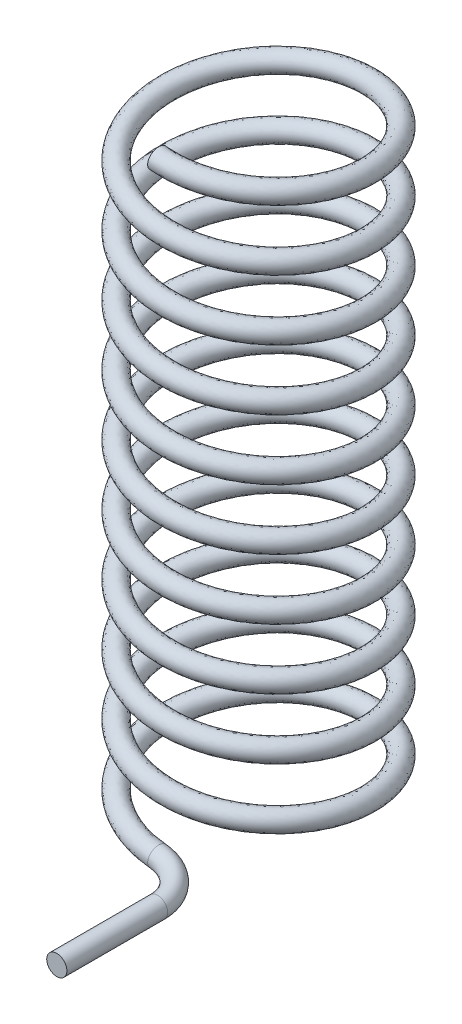
SolidWorks part; units mm, degrees
ref_plane "Ebene vorne" through (0, 0, 0) normal (0, 0, 1) x (1, 0, 0)
ref_plane "Ebene oben" through (0, 0, 0) normal (0, 1, 0) x (1, 0, 0)
ref_plane "Ebene rechts" through (0, 0, 0) normal (1, 0, 0) x (0, 0, -1)
sketch "Skizze2" plane through (0, 0, 0) normal (0, 1, 0) x (1, 0, 0)
  circle A0 centre (0, 0) radius 5
  dimension "D1" = 10
curve "Spirale/Helix1" pitch 3 height 30 turns 10
sketch3d "3D-Skizze1"
  line L1 (1.9909, -0.1901, 7) -> (1.9909, -0.1901, 12)
  arc A0 (0, 0, 5) -> (1.9909, -0.1901, 7) centre (0, 0, 7) ccw
  spline S0 degree 3 poles (-1863.284, 24.4247, -713.0203) (93.82, -4.129, -108.9377) (15.6967, -1.8024, 16.5579) (-3.6271, 0.375, 3.6276) (-4.7398, 0.5625, 1.9632) (-5.1301, 0.75, 0) (-4.7397, 0.9375, -1.9632) (-3.6276, 1.125, -3.6276) (-1.9632, 1.3125, -4.7397) (0, 1.5, -5.1302) (1.9632, 1.6875, -4.7397) (3.6276, 1.875, -3.6276) (4.7397, 2.0625, -1.9632) (5.1302, 2.25, 0) (4.7397, 2.4375, 1.9632) (3.6276, 2.625, 3.6276) (1.9632, 2.8125, 4.7397) (0, 3, 5.1302) (-1.9632, 3.1875, 4.7397) (-3.6276, 3.375, 3.6276) (-4.7397, 3.5625, 1.9632) (-5.1302, 3.75, 0) (-4.7397, 3.9375, -1.9632) (-3.6276, 4.125, -3.6276) (-1.9632, 4.3125, -4.7397) (0, 4.5, -5.1302) (1.9632, 4.6875, -4.7397) (3.6276, 4.875, -3.6276) (4.7397, 5.0625, -1.9632) (5.1302, 5.25, 0) (4.7397, 5.4375, 1.9632) (3.6276, 5.625, 3.6276) (1.9632, 5.8125, 4.7397) (0, 6, 5.1302) (-1.9632, 6.1875, 4.7397) (-3.6276, 6.375, 3.6276) (-4.7397, 6.5625, 1.9632) (-5.1302, 6.75, 0) (-4.7397, 6.9375, -1.9632) (-3.6276, 7.125, -3.6276) (-1.9632, 7.3125, -4.7397) (0, 7.5, -5.1302) (1.9632, 7.6875, -4.7397) (3.6276, 7.875, -3.6276) (4.7397, 8.0625, -1.9632) (5.1302, 8.25, 0) (4.7397, 8.4375, 1.9632) (3.6276, 8.625, 3.6276) (1.9632, 8.8125, 4.7397) (0, 9, 5.1302) (-1.9632, 9.1875, 4.7397) (-3.6276, 9.375, 3.6276) (-4.7397, 9.5625, 1.9632) (-5.1302, 9.75, 0) (-4.7397, 9.9375, -1.9632) (-3.6276, 10.125, -3.6276) (-1.9632, 10.3125, -4.7397) (0, 10.5, -5.1302) (1.9632, 10.6875, -4.7397) (3.6276, 10.875, -3.6276) (4.7397, 11.0625, -1.9632) (5.1302, 11.25, 0) (4.7397, 11.4375, 1.9632) (3.6276, 11.625, 3.6276) (1.9632, 11.8125, 4.7397) (0, 12, 5.1302) (-1.9632, 12.1875, 4.7397) (-3.6276, 12.375, 3.6276) (-4.7397, 12.5625, 1.9632) (-5.1302, 12.75, 0) (-4.7397, 12.9375, -1.9632) (-3.6276, 13.125, -3.6276) (-1.9632, 13.3125, -4.7397) (0, 13.5, -5.1302) (1.9632, 13.6875, -4.7397) (3.6276, 13.875, -3.6276) (4.7397, 14.0625, -1.9632) (5.1302, 14.25, 0) (4.7397, 14.4375, 1.9632) (3.6276, 14.625, 3.6276) (1.9632, 14.8125, 4.7397) (0, 15, 5.1302) (-1.9632, 15.1875, 4.7397) (-3.6276, 15.375, 3.6276) (-4.7397, 15.5625, 1.9632) (-5.1302, 15.75, 0) (-4.7397, 15.9375, -1.9632) (-3.6276, 16.125, -3.6276) (-1.9632, 16.3125, -4.7397) (0, 16.5, -5.1302) (1.9632, 16.6875, -4.7397) (3.6276, 16.875, -3.6276) (4.7397, 17.0625, -1.9632) (5.1302, 17.25, 0) (4.7397, 17.4375, 1.9632) (3.6276, 17.625, 3.6276) (1.9632, 17.8125, 4.7397) (0, 18, 5.1302) (-1.9632, 18.1875, 4.7397) (-3.6276, 18.375, 3.6276) (-4.7397, 18.5625, 1.9632) (-5.1302, 18.75, 0) (-4.7397, 18.9375, -1.9632) (-3.6276, 19.125, -3.6276) (-1.9632, 19.3125, -4.7397) (0, 19.5, -5.1302) (1.9632, 19.6875, -4.7397) (3.6276, 19.875, -3.6276) (4.7397, 20.0625, -1.9632) (5.1302, 20.25, 0) (4.7397, 20.4375, 1.9632) (3.6276, 20.625, 3.6276) (1.9632, 20.8125, 4.7397) (0, 21, 5.1302) (-1.9632, 21.1875, 4.7397) (-3.6276, 21.375, 3.6276) (-4.7397, 21.5625, 1.9632) (-5.1302, 21.75, 0) (-4.7397, 21.9375, -1.9632) (-3.6276, 22.125, -3.6276) (-1.9632, 22.3125, -4.7397) (0, 22.5, -5.1302) (1.9632, 22.6875, -4.7397) (3.6276, 22.875, -3.6276) (4.7397, 23.0625, -1.9632) (5.1302, 23.25, 0) (4.7397, 23.4375, 1.9632) (3.6276, 23.625, 3.6276) (1.9632, 23.8125, 4.7397) (0, 24, 5.1302) (-1.9632, 24.1875, 4.7397) (-3.6276, 24.375, 3.6276) (-4.7397, 24.5625, 1.9632) (-5.1302, 24.75, 0) (-4.7397, 24.9375, -1.9632) (-3.6276, 25.125, -3.6276) (-1.9632, 25.3125, -4.7397) (0, 25.5, -5.1302) (1.9632, 25.6875, -4.7397) (3.6276, 25.875, -3.6276) (4.7397, 26.0625, -1.9632) (5.1302, 26.25, 0) (4.7397, 26.4375, 1.9632) (3.6276, 26.625, 3.6276) (1.9632, 26.8125, 4.7397) (0, 27, 5.1302) (-1.9632, 27.1875, 4.7397) (-3.6276, 27.375, 3.6276) (-4.7397, 27.5625, 1.9632) (-5.1302, 27.75, 0) (-4.7397, 27.9375, -1.9632) (-3.6276, 28.125, -3.6276) (-1.9632, 28.3125, -4.7397) (0, 28.5, -5.1302) (1.9632, 28.6875, -4.7397) (3.6276, 28.875, -3.6276) (4.7397, 29.0625, -1.9632) (5.1301, 29.25, 0) (4.7398, 29.4375, 1.9632) (3.6271, 29.625, 3.6276) (-15.6964, 31.8024, 16.5577) (-93.8175, 34.1289, -108.9337) (1863.1887, 5.5767, -712.9909) knots -0.199259 -0.199259 -0.199259 -0.199259 0.00625 0.0125 0.01875 0.025 0.03125 0.0375 0.04375 0.05 0.05625 0.0625 0.06875 0.075 0.08125 0.0875 0.09375 0.1 0.10625 0.1125 0.11875 0.125 0.13125 0.1375 0.14375 0.15 0.15625 0.1625 0.16875 0.175 0.18125 0.1875 0.19375 0.2 0.20625 0.2125 0.21875 0.225 0.23125 0.2375 0.24375 0.25 0.25625 0.2625 0.26875 0.275 0.28125 0.2875 0.29375 0.3 0.30625 0.3125 0.31875 0.325 0.33125 0.3375 0.34375 0.35 0.35625 0.3625 0.36875 0.375 0.38125 0.3875 0.39375 0.4 0.40625 0.4125 0.41875 0.425 0.43125 0.4375 0.44375 0.45 0.45625 0.4625 0.46875 0.475 0.48125 0.4875 0.49375 0.5 0.50625 0.5125 0.51875 0.525 0.53125 0.5375 0.54375 0.55 0.55625 0.5625 0.56875 0.575 0.58125 0.5875 0.59375 0.6 0.60625 0.6125 0.61875 0.625 0.63125 0.6375 0.64375 0.65 0.65625 0.6625 0.66875 0.675 0.68125 0.6875 0.69375 0.7 0.70625 0.7125 0.71875 0.725 0.73125 0.7375 0.74375 0.75 0.75625 0.7625 0.76875 0.775 0.78125 0.7875 0.79375 0.8 0.80625 0.8125 0.81875 0.825 0.83125 0.8375 0.84375 0.85 0.85625 0.8625 0.86875 0.875 0.88125 0.8875 0.89375 0.9 0.90625 0.9125 0.91875 0.925 0.93125 0.9375 0.94375 0.95 0.95625 0.9625 0.96875 0.975 0.98125 0.9875 0.99375 1.199256 1.199256 1.199256 1.199256 only from (0, 0, 5) to (0, 30, 5) construction
  spline S1 degree 3 poles (0, 0, 5) (-0.6503, 0.0621, 5) (-1.9651, 0.1877, 4.7397) (-3.6271, 0.375, 3.6276) (-4.7398, 0.5625, 1.9632) (-5.1301, 0.75, 0) (-4.7397, 0.9375, -1.9632) (-3.6276, 1.125, -3.6276) (-1.9632, 1.3125, -4.7397) (0, 1.5, -5.1302) (1.9632, 1.6875, -4.7397) (3.6276, 1.875, -3.6276) (4.7397, 2.0625, -1.9632) (5.1302, 2.25, 0) (4.7397, 2.4375, 1.9632) (3.6276, 2.625, 3.6276) (1.9632, 2.8125, 4.7397) (0, 3, 5.1302) (-1.9632, 3.1875, 4.7397) (-3.6276, 3.375, 3.6276) (-4.7397, 3.5625, 1.9632) (-5.1302, 3.75, 0) (-4.7397, 3.9375, -1.9632) (-3.6276, 4.125, -3.6276) (-1.9632, 4.3125, -4.7397) (0, 4.5, -5.1302) (1.9632, 4.6875, -4.7397) (3.6276, 4.875, -3.6276) (4.7397, 5.0625, -1.9632) (5.1302, 5.25, 0) (4.7397, 5.4375, 1.9632) (3.6276, 5.625, 3.6276) (1.9632, 5.8125, 4.7397) (0, 6, 5.1302) (-1.9632, 6.1875, 4.7397) (-3.6276, 6.375, 3.6276) (-4.7397, 6.5625, 1.9632) (-5.1302, 6.75, 0) (-4.7397, 6.9375, -1.9632) (-3.6276, 7.125, -3.6276) (-1.9632, 7.3125, -4.7397) (0, 7.5, -5.1302) (1.9632, 7.6875, -4.7397) (3.6276, 7.875, -3.6276) (4.7397, 8.0625, -1.9632) (5.1302, 8.25, 0) (4.7397, 8.4375, 1.9632) (3.6276, 8.625, 3.6276) (1.9632, 8.8125, 4.7397) (0, 9, 5.1302) (-1.9632, 9.1875, 4.7397) (-3.6276, 9.375, 3.6276) (-4.7397, 9.5625, 1.9632) (-5.1302, 9.75, 0) (-4.7397, 9.9375, -1.9632) (-3.6276, 10.125, -3.6276) (-1.9632, 10.3125, -4.7397) (0, 10.5, -5.1302) (1.9632, 10.6875, -4.7397) (3.6276, 10.875, -3.6276) (4.7397, 11.0625, -1.9632) (5.1302, 11.25, 0) (4.7397, 11.4375, 1.9632) (3.6276, 11.625, 3.6276) (1.9632, 11.8125, 4.7397) (0, 12, 5.1302) (-1.9632, 12.1875, 4.7397) (-3.6276, 12.375, 3.6276) (-4.7397, 12.5625, 1.9632) (-5.1302, 12.75, 0) (-4.7397, 12.9375, -1.9632) (-3.6276, 13.125, -3.6276) (-1.9632, 13.3125, -4.7397) (0, 13.5, -5.1302) (1.9632, 13.6875, -4.7397) (3.6276, 13.875, -3.6276) (4.7397, 14.0625, -1.9632) (5.1302, 14.25, 0) (4.7397, 14.4375, 1.9632) (3.6276, 14.625, 3.6276) (1.9632, 14.8125, 4.7397) (0, 15, 5.1302) (-1.9632, 15.1875, 4.7397) (-3.6276, 15.375, 3.6276) (-4.7397, 15.5625, 1.9632) (-5.1302, 15.75, 0) (-4.7397, 15.9375, -1.9632) (-3.6276, 16.125, -3.6276) (-1.9632, 16.3125, -4.7397) (0, 16.5, -5.1302) (1.9632, 16.6875, -4.7397) (3.6276, 16.875, -3.6276) (4.7397, 17.0625, -1.9632) (5.1302, 17.25, 0) (4.7397, 17.4375, 1.9632) (3.6276, 17.625, 3.6276) (1.9632, 17.8125, 4.7397) (0, 18, 5.1302) (-1.9632, 18.1875, 4.7397) (-3.6276, 18.375, 3.6276) (-4.7397, 18.5625, 1.9632) (-5.1302, 18.75, 0) (-4.7397, 18.9375, -1.9632) (-3.6276, 19.125, -3.6276) (-1.9632, 19.3125, -4.7397) (0, 19.5, -5.1302) (1.9632, 19.6875, -4.7397) (3.6276, 19.875, -3.6276) (4.7397, 20.0625, -1.9632) (5.1302, 20.25, 0) (4.7397, 20.4375, 1.9632) (3.6276, 20.625, 3.6276) (1.9632, 20.8125, 4.7397) (0, 21, 5.1302) (-1.9632, 21.1875, 4.7397) (-3.6276, 21.375, 3.6276) (-4.7397, 21.5625, 1.9632) (-5.1302, 21.75, 0) (-4.7397, 21.9375, -1.9632) (-3.6276, 22.125, -3.6276) (-1.9632, 22.3125, -4.7397) (0, 22.5, -5.1302) (1.9632, 22.6875, -4.7397) (3.6276, 22.875, -3.6276) (4.7397, 23.0625, -1.9632) (5.1302, 23.25, 0) (4.7397, 23.4375, 1.9632) (3.6276, 23.625, 3.6276) (1.9632, 23.8125, 4.7397) (0, 24, 5.1302) (-1.9632, 24.1875, 4.7397) (-3.6276, 24.375, 3.6276) (-4.7397, 24.5625, 1.9632) (-5.1302, 24.75, 0) (-4.7397, 24.9375, -1.9632) (-3.6276, 25.125, -3.6276) (-1.9632, 25.3125, -4.7397) (0, 25.5, -5.1302) (1.9632, 25.6875, -4.7397) (3.6276, 25.875, -3.6276) (4.7397, 26.0625, -1.9632) (5.1302, 26.25, 0) (4.7397, 26.4375, 1.9632) (3.6276, 26.625, 3.6276) (1.9632, 26.8125, 4.7397) (0, 27, 5.1302) (-1.9632, 27.1875, 4.7397) (-3.6276, 27.375, 3.6276) (-4.7397, 27.5625, 1.9632) (-5.1302, 27.75, 0) (-4.7397, 27.9375, -1.9632) (-3.6276, 28.125, -3.6276) (-1.9632, 28.3125, -4.7397) (0, 28.5, -5.1302) (1.9632, 28.6875, -4.7397) (3.6276, 28.875, -3.6276) (4.7397, 29.0625, -1.9632) (5.1301, 29.25, 0) (4.7398, 29.4375, 1.9632) (3.6271, 29.625, 3.6276) (1.965, 29.8123, 4.7397) (0.6501, 29.9379, 5.0001) (-0.0004, 30, 5) knots 0 0 0 0 0.00625 0.0125 0.01875 0.025 0.03125 0.0375 0.04375 0.05 0.05625 0.0625 0.06875 0.075 0.08125 0.0875 0.09375 0.1 0.10625 0.1125 0.11875 0.125 0.13125 0.1375 0.14375 0.15 0.15625 0.1625 0.16875 0.175 0.18125 0.1875 0.19375 0.2 0.20625 0.2125 0.21875 0.225 0.23125 0.2375 0.24375 0.25 0.25625 0.2625 0.26875 0.275 0.28125 0.2875 0.29375 0.3 0.30625 0.3125 0.31875 0.325 0.33125 0.3375 0.34375 0.35 0.35625 0.3625 0.36875 0.375 0.38125 0.3875 0.39375 0.4 0.40625 0.4125 0.41875 0.425 0.43125 0.4375 0.44375 0.45 0.45625 0.4625 0.46875 0.475 0.48125 0.4875 0.49375 0.5 0.50625 0.5125 0.51875 0.525 0.53125 0.5375 0.54375 0.55 0.55625 0.5625 0.56875 0.575 0.58125 0.5875 0.59375 0.6 0.60625 0.6125 0.61875 0.625 0.63125 0.6375 0.64375 0.65 0.65625 0.6625 0.66875 0.675 0.68125 0.6875 0.69375 0.7 0.70625 0.7125 0.71875 0.725 0.73125 0.7375 0.74375 0.75 0.75625 0.7625 0.76875 0.775 0.78125 0.7875 0.79375 0.8 0.80625 0.8125 0.81875 0.825 0.83125 0.8375 0.84375 0.85 0.85625 0.8625 0.86875 0.875 0.88125 0.8875 0.89375 0.9 0.90625 0.9125 0.91875 0.925 0.93125 0.9375 0.94375 0.95 0.95625 0.9625 0.96875 0.975 0.98125 0.9875 0.99375 1.000001 1.000001 1.000001 1.000001
  point P5 (-0.1901, -1.9909, 7)
  point P7 (0, 0, 0)
  dimension "D2" = 5
  dimension "D1" = 2
ref_plane "Ebene1" through (1.9909, -0.1901, 12) normal (0, 0, 1) x (1, 0, 0)
sketch "Skizze3" plane through (1.9909, -0.1901, 12) normal (0, 0, 1) x (1, 0, 0)
  circle A0 centre (0, 0) radius 0.5
  dimension "D1" = 1
sweep "Austragung1" add profiles "Skizze3" path "3D-Skizze1"
